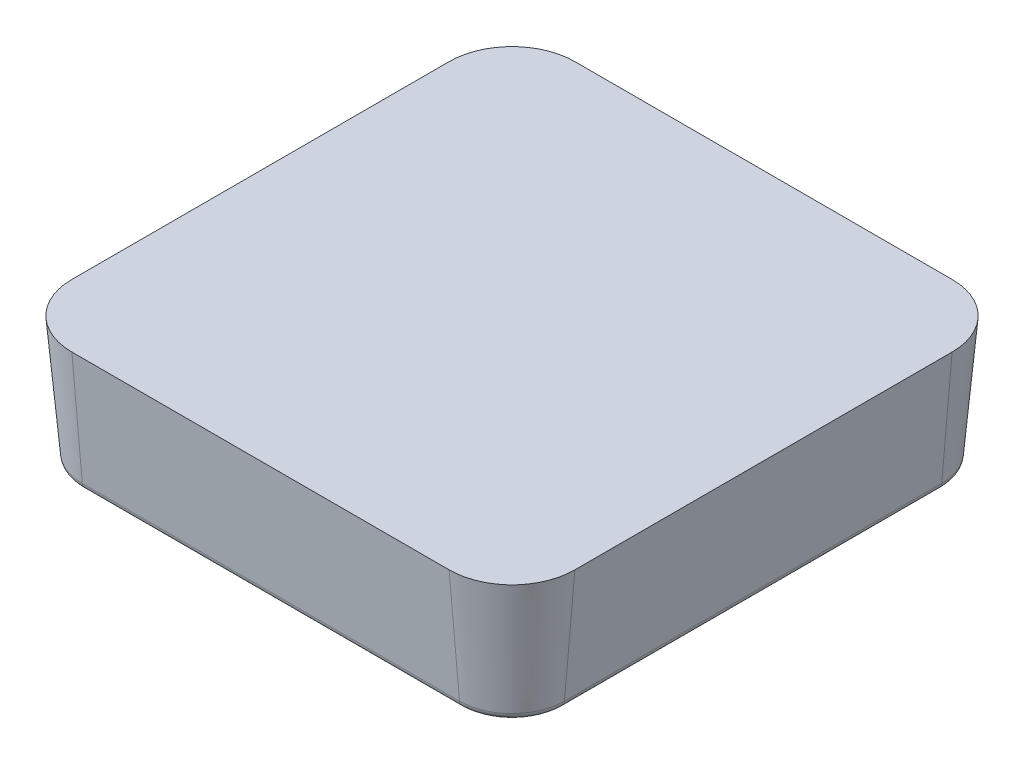
SolidWorks part; units mm, degrees
material "CA"
ref_plane "Front Plane" through (0, 0, 0) normal (0, 0, 1) x (1, 0, 0)
ref_plane "Top Plane" through (0, 0, 0) normal (0, 1, 0) x (1, 0, 0)
ref_plane "Right Plane" through (0, 0, 0) normal (1, 0, 0) x (0, 0, -1)
sketch "Sketch1" plane through (0, 0, 0) normal (0, 1, 0) x (1, 0, 0)
  line L1 (-9.525, -12.7) -> (9.525, -12.7)
  line L2 (-12.7, -9.525) -> (-12.7, 9.525)
  line L3 (-9.525, 12.7) -> (9.525, 12.7)
  line L4 (12.7, -9.525) -> (12.7, 9.525)
  line L5 (-12.7, -12.7) -> (12.7, 12.7) construction
  line L6 (-12.7, 12.7) -> (12.7, -12.7) construction
  arc A0 (-9.525, -12.7) -> (-12.7, -9.525) centre (-9.525, -9.525) cw
  arc A1 (9.525, -12.7) -> (12.7, -9.525) centre (9.525, -9.525) ccw
  arc A2 (9.525, 12.7) -> (12.7, 9.525) centre (9.525, 9.525) cw
  arc A3 (-12.7, 9.525) -> (-9.525, 12.7) centre (-9.525, 9.525) cw
  point P0 (0, 0)
  dimension "D3" = 3.175
  dimension "D1" = 25.4
  dimension "D2" = 25.4
extrude "Boss-Extrude1" add sketch "Sketch1" against normal blind 6.35 draft 5
sketch "Sketch6" plane through (0, 0, 0) normal (0, 0, 1) x (1, 0, 0)
  line L0 (0, 0) -> (0, -2.159) construction
  line L1 (0, -2.159) -> (-7.366, -9.525)
  line L2 (0, -2.159) -> (7.366, -9.525)
  line L3 (-7.366, -9.525) -> (7.366, -9.525)
  line L4 (-9.525, 0) -> (9.525, 0) construction
  dimension "D1" = 2.159
  dimension "D2" = 90
  dimension "D3" = 9.525
extrude "Cut-Extrude3" cut sketch "Sketch6" against normal through all
pattern_circular "CirPattern3" count 18 over 360 about axis through (0, 0, 0) along (0, 1, 0) of "Cut-Extrude3"
sketch "Sketch7" plane through (0, 0, 0) normal (0, 1, 0) x (1, 0, 0)
  line L4 (-9.525, -12.7) -> (9.525, -12.7)
  line L5 (12.7, -9.525) -> (12.7, 9.525)
  line L6 (9.525, 12.7) -> (-9.525, 12.7)
  line L7 (-12.7, 9.525) -> (-12.7, -9.525)
  line L8 (-9.525, -12.7) -> (9.525, -12.7)
  line L9 (12.7, -9.525) -> (12.7, 9.525)
  line L10 (9.525, 12.7) -> (-9.525, 12.7)
  line L11 (-12.7, 9.525) -> (-12.7, -9.525)
  line L20 (-9.525, -10.668) -> (9.525, -10.668)
  line L21 (10.668, -9.525) -> (10.668, 9.525)
  line L22 (9.525, 10.668) -> (-9.525, 10.668)
  line L23 (-10.668, 9.525) -> (-10.668, -9.525)
  line L24 (-9.525, -10.668) -> (9.525, -10.668)
  line L25 (10.668, -9.525) -> (10.668, 9.525)
  line L26 (9.525, 10.668) -> (-9.525, 10.668)
  line L27 (-10.668, 9.525) -> (-10.668, -9.525)
  arc A4 (-12.7, -9.525) -> (-9.525, -12.7) centre (-9.525, -9.525) ccw
  arc A5 (9.525, -12.7) -> (12.7, -9.525) centre (9.525, -9.525) ccw
  arc A6 (12.7, 9.525) -> (9.525, 12.7) centre (9.525, 9.525) ccw
  arc A7 (-9.525, 12.7) -> (-12.7, 9.525) centre (-9.525, 9.525) ccw
  arc A8 (-12.7, -9.525) -> (-9.525, -12.7) centre (-9.525, -9.525) ccw
  arc A9 (9.525, -12.7) -> (12.7, -9.525) centre (9.525, -9.525) ccw
  arc A10 (12.7, 9.525) -> (9.525, 12.7) centre (9.525, 9.525) ccw
  arc A11 (-9.525, 12.7) -> (-12.7, 9.525) centre (-9.525, 9.525) ccw
  arc A20 (-10.668, -9.525) -> (-9.525, -10.668) centre (-9.525, -9.525) ccw
  arc A21 (9.525, -10.668) -> (10.668, -9.525) centre (9.525, -9.525) ccw
  arc A22 (10.668, 9.525) -> (9.525, 10.668) centre (9.525, 9.525) ccw
  arc A23 (-9.525, 10.668) -> (-10.668, 9.525) centre (-9.525, 9.525) ccw
  arc A24 (-10.668, -9.525) -> (-9.525, -10.668) centre (-9.525, -9.525) ccw
  arc A25 (9.525, -10.668) -> (10.668, -9.525) centre (9.525, -9.525) ccw
  arc A26 (10.668, 9.525) -> (9.525, 10.668) centre (9.525, 9.525) ccw
  arc A27 (-9.525, 10.668) -> (-10.668, 9.525) centre (-9.525, 9.525) ccw
  dimension "D1" = 0
  dimension "D2" = 2.032
extrude "Boss-Extrude3" add sketch "Sketch7" against normal blind 6.35 draft 5
fillet "Fillet2" radius 0.381 16 edges at (-11.3772, -6.35, -11.3772) (-11.3772, -6.35, 11.3772) (-12.1444, -6.35, 0) (0, -6.35, 12.1444) (11.3772, -6.35, 11.3772) (12.1444, -6.35, 0) (11.3772, -6.35, -11.3772) (0, -6.35, -12.1444) (-11.2236, -6.35, 0) (-10.7261, -6.35, 10.7261) (0, -6.35, 11.2236) (10.7261, -6.35, 10.7261) (11.2236, -6.35, 0) (10.7261, -6.35, -10.7261) (0, -6.35, -11.2236) (-10.7261, -6.35, -10.7261)
ref_plane "Plane1" through (0, -5.969, 0) normal (0, -1, 0) x (-1, 0, 0)
sketch "Sketch8" plane through (0, -5.969, 0) normal (0, -1, 0) x (-1, 0, 0)
  line L0 (0, 0) -> (0, 13.8845) construction
  circle A0 centre (0, 10.668) radius 1.1811
  dimension "D1" = 2.3622
  dimension "D2" = 10.668
extrude "Boss-Extrude4" add sketch "Sketch8" against normal through all
sketch "Sketch9" plane through (0, -5.969, 0) normal (0, -1, 0) x (1, 0, 0)
  circle A0 centre (0, -10.668) radius 1.1811
extrude "Cut-Extrude4" cut sketch "Sketch9" along normal through all
sketch "Sketch10" plane through (0, 0, 0) normal (0, 0, 1) x (1, 0, 0)
  line L0 (0, 0) -> (0, 16.2069) construction
pattern_circular "CirPattern4" count 4 over 360 about axis through (0, 0, 0) along (0, 1, 0) of "Cut-Extrude4", "Boss-Extrude4"
sketch "Sketch11 - OFFSET .005" plane through (0, 0, 0) normal (0, 1, 0) x (1, 0, 0)
  line L8 (-9.525, -12.827) -> (9.525, -12.827)
  line L9 (12.827, -9.525) -> (12.827, 9.525)
  line L10 (9.525, 12.827) -> (-9.525, 12.827)
  line L11 (-12.827, 9.525) -> (-12.827, -9.525)
  line L12 (-9.525, -12.827) -> (9.525, -12.827) construction
  line L13 (12.827, -9.525) -> (12.827, 9.525) construction
  line L14 (9.525, 12.827) -> (-9.525, 12.827) construction
  line L15 (-12.827, 9.525) -> (-12.827, -9.525) construction
  arc A8 (-12.827, -9.525) -> (-9.525, -12.827) centre (-9.525, -9.525) ccw
  arc A9 (9.525, -12.827) -> (12.827, -9.525) centre (9.525, -9.525) ccw
  arc A10 (12.827, 9.525) -> (9.525, 12.827) centre (9.525, 9.525) ccw
  arc A11 (-9.525, 12.827) -> (-12.827, 9.525) centre (-9.525, 9.525) ccw
  arc A12 (-12.827, -9.525) -> (-9.525, -12.827) centre (-9.525, -9.525) ccw construction
  arc A13 (9.525, -12.827) -> (12.827, -9.525) centre (9.525, -9.525) ccw construction
  arc A14 (12.827, 9.525) -> (9.525, 12.827) centre (9.525, 9.525) ccw construction
  arc A15 (-9.525, 12.827) -> (-12.827, 9.525) centre (-9.525, 9.525) ccw construction
  dimension "D1" = 0.127
